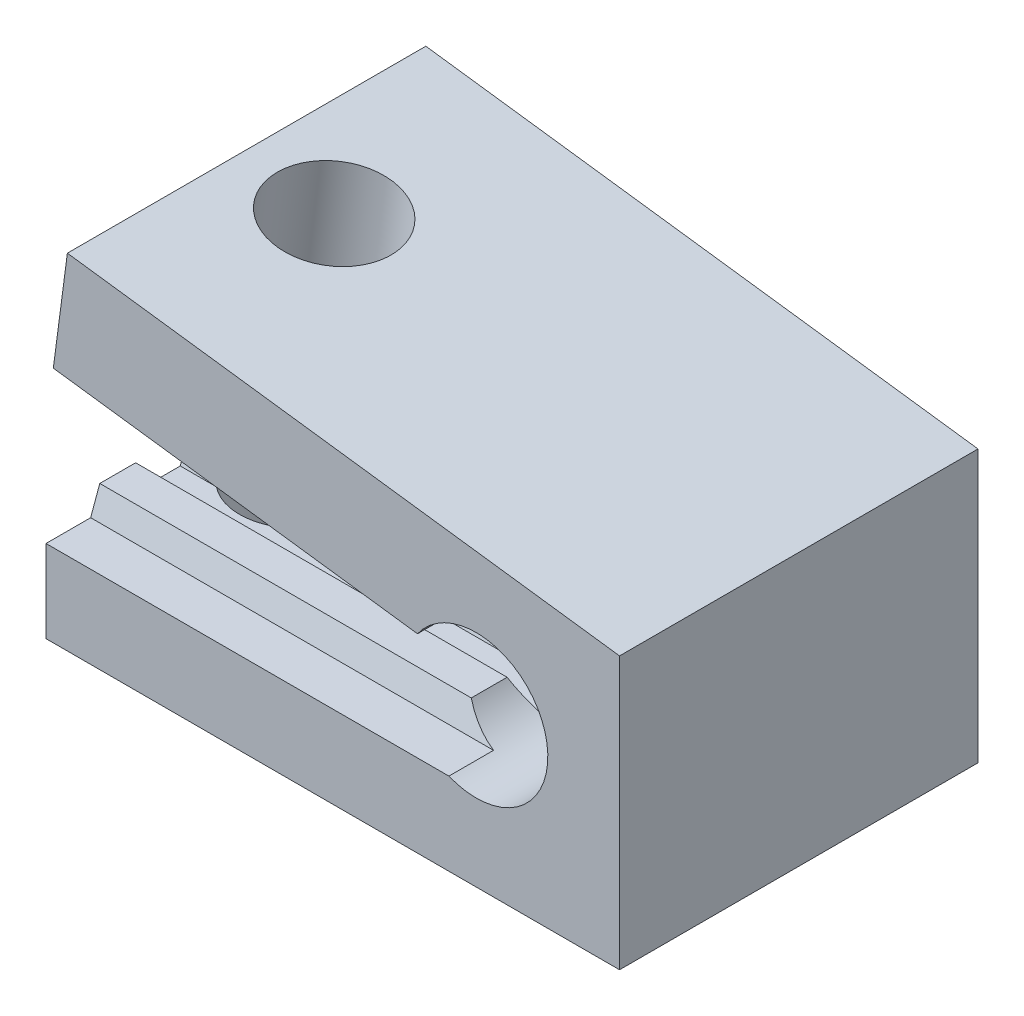
SolidWorks part; units mm, degrees
ref_plane "Front Plane" through (0, 0, 0) normal (0, 0, 1) x (1, 0, 0)
ref_plane "Top Plane" through (0, 0, 0) normal (0, 1, 0) x (1, 0, 0)
ref_plane "Right Plane" through (0, 0, 0) normal (1, 0, 0) x (0, 0, -1)
sketch "Sketch1" plane through (0, 0, 0) normal (0, 0, 1) x (1, 0, 0)
  line L0 (4, 6.0839) -> (-11.404, 8.1118)
  line L1 (4, -1.5) -> (-12, -1.5)
  line L2 (4, -1.5) -> (4, 6.0839)
  line L3 (-1.6363, 1.5) -> (-12, 1.5)
  line L4 (-12, -1.5) -> (-12, 1.5)
  line L5 (-12, 0) -> (4, 0) construction
  line L6 (55, 0) -> (-55, 0) construction
  line L9 (-1.6363, 3.8) -> (-11.7955, 5.1375)
  line L10 (0, -55) -> (0, 55) construction
  line L11 (-11.7955, 5.1375) -> (-11.404, 8.1118)
  arc A0 (-1.6363, 1.5) -> (-1.6363, 3.8) centre (0, 2.65) ccw
  arc A1 (-11.7955, 5.1375) -> (-12, 1.5) centre (0, 2.65) ccw construction
  point P0 (0, 0)
  point P6 (0, 2.9376)
  point P13 (0, 0)
  dimension "D6" = 2
  dimension "D4" = 2.3
  dimension "D1" = 16
  dimension "D2" = 3
  dimension "D3" = 7.5
  dimension "D5" = 12
extrude "Boss-Extrude1" add sketch "Sketch1" along normal mid plane 10
sketch "Sketch2" plane through (0, 0, 5) normal (0, 0, 1) x (1, 0, 0)
  line L0 (-12.2548, 0.8) -> (-12, 1.5)
  line L2 (-1.6363, 1.5) -> (-12, 1.5) construction
  line L3 (-12, 1.5) -> (-11, 1.5)
  line L4 (-11, 1.5) -> (-10.7452, 0.8)
  line L5 (-11.5, 1.5) -> (-11.5, 0.8) construction
  line L6 (-9.7548, 0.8) -> (-9.5, 1.5)
  line L7 (-8.5, 1.5) -> (-8.2452, 0.8)
  line L8 (-9.5, 1.5) -> (-8.5, 1.5)
  line L9 (-7.2548, 0.8) -> (-7, 1.5)
  line L10 (-6, 1.5) -> (-5.7452, 0.8)
  line L11 (-7, 1.5) -> (-6, 1.5)
  line L12 (-4.7548, 0.8) -> (-4.5, 1.5)
  line L13 (-3.5, 1.5) -> (-3.2452, 0.8)
  line L14 (-4.5, 1.5) -> (-3.5, 1.5)
  line L15 (-2.2548, 0.8) -> (-2, 1.5)
  line L17 (-2, 1.5) -> (-1, 1.5)
  line L18 (-10.7452, 0.8) -> (-9.7548, 0.8)
  line L19 (-8.2452, 0.8) -> (-7.2548, 0.8)
  line L20 (-5.7452, 0.8) -> (-4.7548, 0.8)
  line L21 (-3.2452, 0.8) -> (-2.2548, 0.8)
  line L22 (-1, 1.5) -> (-0.7452, 0.8) [skipped]
  dimension "D1" = 1
  dimension "D2" = 40
  dimension "D3" = 0.7
  dimension "D4" = 5
extrude "Cut-Extrude11" [suppressed] cut sketch "Sketch2" against normal through all and the other way through all
sketch "Sketch3" plane through (0, 0, 5) normal (0, 0, 1) x (1, 0, 0)
  line L0 (-12.0889, 4.7671) -> (-12, 4.0275)
  line L1 (-12, 4.0275) -> (-11.0262, 3.8)
  line L2 (-12, 3.8) -> (-1.6363, 3.8) construction
  line L3 (-11.0262, 3.8) -> (-10.6189, 4.4237)
  line L4 (-11.5131, 3.9137) -> (-10.7004, 7.3931) construction
  line L6 (-9.6544, 4.1984) -> (-9.5655, 3.4588)
  line L7 (-9.5655, 3.4588) -> (-8.5917, 3.2314)
  line L8 (-8.5917, 3.2314) -> (-8.1844, 3.8551)
  line L9 (-7.2199, 3.6298) -> (-7.1311, 2.8902)
  line L10 (-7.1311, 2.8902) -> (-6.1573, 2.6627)
  line L11 (-6.1573, 2.6627) -> (-5.7499, 3.2864)
  line L12 (-4.7855, 3.0612) -> (-4.6966, 2.3216)
  line L13 (-4.6966, 2.3216) -> (-3.7228, 2.0941)
  line L14 (-3.7228, 2.0941) -> (-3.3155, 2.7178)
  line L15 (-2.351, 2.4925) -> (-2.2621, 1.7529)
  line L16 (-2.2621, 1.7529) -> (-1.2883, 1.5255)
  line L17 (-1.2883, 1.5255) -> (-0.881, 2.1492)
  line L18 (-10.6189, 4.4237) -> (-9.6544, 4.1984)
  line L19 (-8.1844, 3.8551) -> (-7.2199, 3.6298)
  line L20 (-5.7499, 3.2864) -> (-4.7855, 3.0612)
  line L21 (-3.3155, 2.7178) -> (-2.351, 2.4925)
  line L23 (-12, 6.8) -> (-12, 3.8) construction
  dimension "D1" = 1
  dimension "D2" = 40
  dimension "D3" = 0.7
  dimension "D4" = 5
extrude "Cut-Extrude4" [suppressed] cut sketch "Sketch3" against normal through all and the other way through all flip side to cut
sketch "Sketch4" plane through (0.8555, 6.4978, 0) normal (0.1305, 0.9914, 0) x (0.9914, -0.1305, 0)
  line L0 (-55, 0) -> (55, 0) construction
  line L1 (-12, -5) -> (-12, 5) construction
  circle A0 centre (-9.9, 0) radius 1.6
  dimension "D1" = 3.2
  dimension "D2" = 2.1
extrude "Cut-Extrude5" cut sketch "Sketch4" against normal up to next
sketch "Sketch5" plane through (0, -1.5, 0) normal (0, -1, 0) x (1, 0, 0)
  line L0 (55, 0) -> (-55, 0) construction
  line L1 (-12, 5) -> (-12, -5) construction
  circle A0 centre (-10, 0) radius 1.6
  dimension "D1" = 3.2
  dimension "D2" = 2
extrude "Cut-Extrude6" cut sketch "Sketch5" against normal up to next
sketch "Sketch6" plane through (-12, 0, 0) normal (-1, 0, 0) x (0, 0, 1)
  line L0 (-5, 1.5) -> (-5.2548, 0.8)
  line L1 (-5, 1.5) -> (-4, 1.5)
  line L2 (5, 1.5) -> (-5, 1.5) construction
  line L3 (-4, 1.5) -> (-3.7452, 0.8)
  line L4 (-4.5, 1.5) -> (-4.5, 0.6928) construction
  line L5 (-1.5, 1.5) -> (-1.2452, 0.8)
  line L6 (-2.5, 1.5) -> (-1.5, 1.5)
  line L7 (-2.5, 1.5) -> (-2.7548, 0.8)
  line L8 (1, 1.5) -> (1.2548, 0.8)
  line L9 (0, 1.5) -> (1, 1.5)
  line L10 (0, 1.5) -> (-0.2548, 0.8)
  line L11 (3.5, 1.5) -> (3.7548, 0.8)
  line L12 (2.5, 1.5) -> (3.5, 1.5)
  line L13 (2.5, 1.5) -> (2.2452, 0.8)
  line L14 (-3.7452, 0.8) -> (-2.7548, 0.8)
  line L15 (-1.2452, 0.8) -> (-0.2548, 0.8)
  line L16 (5, 1.5) -> (5, -1.5) construction
  line L17 (3.7548, 0.8) -> (5, 0.8)
  line L18 (1.2548, 0.8) -> (2.2452, 0.8)
  dimension "D1" = 40
  dimension "D2" = 0.7
  dimension "D3" = 1
  dimension "D4" = 4
extrude "Cut-Extrude12" cut sketch "Sketch6" against normal blind 12 and the other way through all
